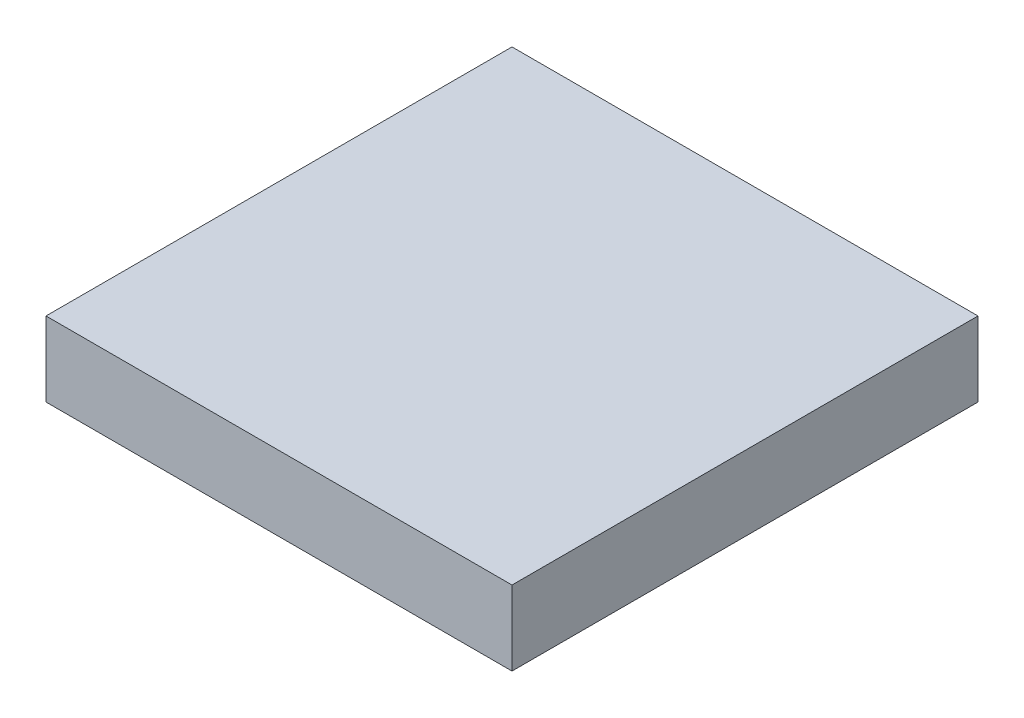
SolidWorks part; units mm, degrees
ref_plane "Front Plane" through (0, 0, 0) normal (0, 0, 1) x (1, 0, 0)
ref_plane "Top Plane" through (0, 0, 0) normal (0, 1, 0) x (1, 0, 0)
ref_plane "Right Plane" through (0, 0, 0) normal (1, 0, 0) x (0, 0, -1)
sketch "Sketch1" plane through (0, 0, 0) normal (0, 1, 0) x (1, 0, 0)
  line L1 (-9.525, -9.525) -> (9.525, -9.525)
  line L2 (-9.525, -9.525) -> (-9.525, 9.525)
  line L3 (-9.525, 9.525) -> (9.525, 9.525)
  line L4 (9.525, -9.525) -> (9.525, 9.525)
  line L5 (-9.525, -9.525) -> (9.525, 9.525) construction
  line L6 (-9.525, 9.525) -> (9.525, -9.525) construction
  point P0 (0, 0)
extrude "Boss-Extrude1" add sketch "Sketch1" along normal blind 3.048
